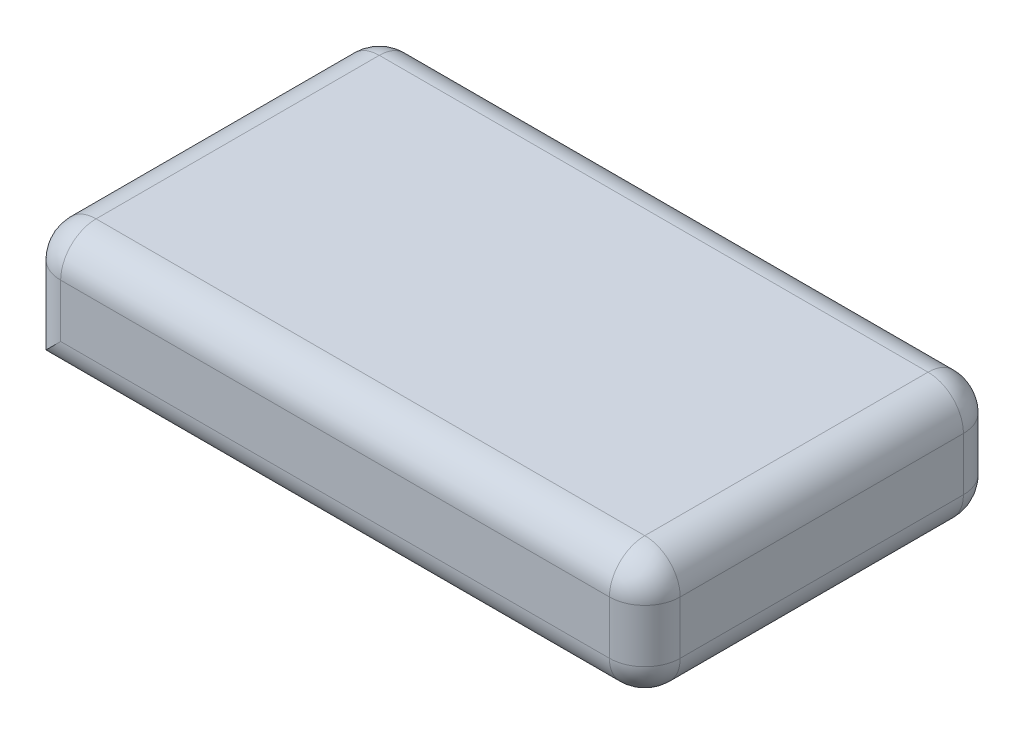
SolidWorks part; units mm, degrees
ref_plane "Alzado" through (0, 0, 0) normal (0, 0, 1) x (1, 0, 0)
ref_plane "Planta" through (0, 0, 0) normal (0, 1, 0) x (1, 0, 0)
ref_plane "Vista lateral" through (0, 0, 0) normal (1, 0, 0) x (0, 0, -1)
sketch "Croquis1" plane through (0, 0, 0) normal (0, 1, 0) x (1, 0, 0)
  line L1 (-17.5, -10) -> (17.5, -10)
  line L2 (-17.5, -10) -> (-17.5, 10)
  line L3 (-17.5, 10) -> (17.5, 10)
  line L4 (17.5, -10) -> (17.5, 10)
  line L5 (-17.5, -10) -> (17.5, 10) construction
  line L6 (-17.5, 10) -> (17.5, -10) construction
  point P0 (0, 0)
  dimension "D1" = 35
  dimension "D2" = 20
extrude "Saliente-Extruir1" add sketch "Croquis1" along normal blind 7
fillet "Redondeo1" radius 2 11 edges at (-17.5, 3.5, -10) (0, 0, 10) (0, 0, -10) (0, 7, -10) (17.5, 3.5, -10) (17.5, 0, 0) (17.5, 7, 0) (17.5, 3.5, 10) (-17.5, 3.5, 10) (-17.5, 7, 0) (0, 7, 10)
